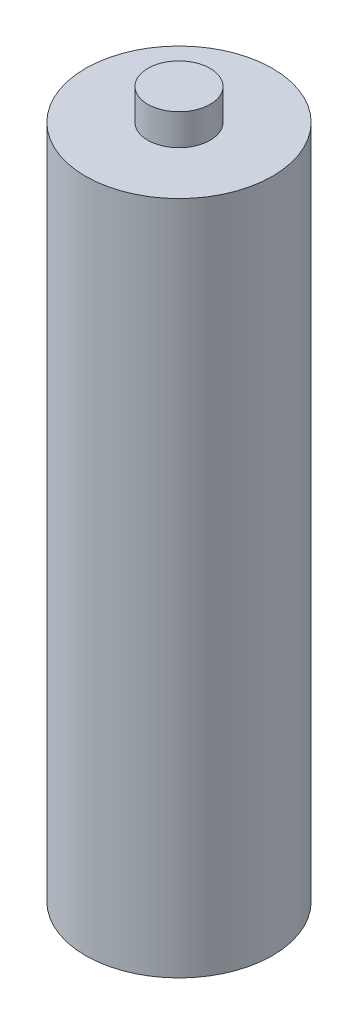
SolidWorks part; units mm, degrees
ref_plane "Front Plane" through (0, 0, 0) normal (0, 0, 1) x (1, 0, 0)
ref_plane "Top Plane" through (0, 0, 0) normal (0, 1, 0) x (1, 0, 0)
ref_plane "Right Plane" through (0, 0, 0) normal (1, 0, 0) x (0, 0, -1)
sketch "Sketch1" plane through (0, 0, 0) normal (0, 1, 0) x (1, 0, 0)
  circle A0 centre (0, 0) radius 9
  dimension "D1" = 18
extrude "Boss-Extrude1" add sketch "Sketch1" along normal blind 65
sketch "Sketch2" plane through (0, 65, 0) normal (0, 1, 0) x (1, 0, 0)
  circle A0 centre (0, 0) radius 3
  dimension "D1" = 6
extrude "Boss-Extrude2" add sketch "Sketch2" along normal blind 3
